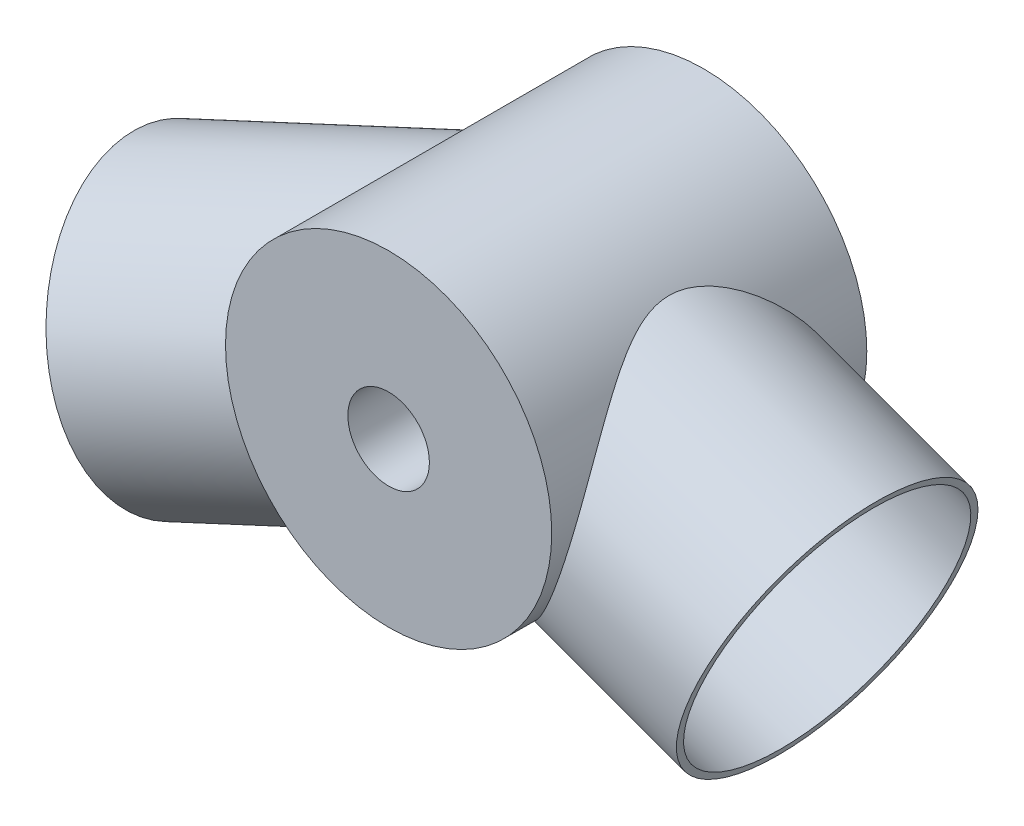
SolidWorks part; units mm, degrees
material "ABS"
ref_plane "Front Plane" through (0, 0, 0) normal (0, 0, 1) x (1, 0, 0)
ref_plane "Top Plane" through (0, 0, 0) normal (0, 1, 0) x (1, 0, 0)
ref_plane "Right Plane" through (0, 0, 0) normal (1, 0, 0) x (0, 0, -1)
sketch "Sketch1" plane through (0, 0, 0) normal (0, 0, 1) x (1, 0, 0)
  circle A0 centre (0, 0) radius 12
  dimension "D1" = 24
extrude "Boss-Extrude1" add sketch "Sketch1" along normal mid plane 23.18
sketch "Sketch2" plane through (0, 0, 0) normal (1, 0, 0) x (0, 0, -1)
  line L0 (-11.59, 0) -> (11.59, 0) construction
  line L1 (11.59, -12) -> (11.59, 12) construction
  point P6 (0, 0)
ref_plane "Plane1" through (0, 0, 0) normal (0.9397, -0.342, 0) x (0, 0, -1)
ref_plane "Plane2" through (0, 0, 0) normal (0.9397, 0.342, 0) x (0, 0, -1)
sketch "Sketch6" plane through (0, 0, 0) normal (0.9397, 0.342, 0) x (0, 0, -1)
  line L0 (0, -12) -> (0, 12) construction
  line L2 (11.59, 12) -> (-11.59, 12) construction
  point P4 (0, 0)
ref_plane "Plane3" through (0, 0, 0) normal (0.9254, 0.3368, -0.1736) x (-0.342, 0.9397, 0)
sketch "Sketch8" plane through (0, 0, 0) normal (0.9254, 0.3368, -0.1736) x (-0.342, 0.9397, 0)
  circle A0 centre (0, -1.5) radius 10
  dimension "D1" = 20
  dimension "D2" = 1.5
extrude "Extrude-Thin2" add sketch "Sketch8" against normal blind 22 from offset 4.1 thin offset against normal yes
sketch "Sketch3" plane through (0, 0, 0) normal (0.9397, -0.342, 0) x (0, 0, -1)
  circle A0 centre (0, 0) radius 10
  dimension "D1" = 20
extrude "Extrude-Thin1" add sketch "Sketch3" along normal blind 22 thin
sketch "Sketch4" plane through (0, 0, -11.59) normal (0, 0, -1) x (-1, 0, 0)
  circle A0 centre (0, 0) radius 7.5
  dimension "D1" = 15
extrude "Cut-Extrude1" cut sketch "Sketch4" against normal blind 10
sketch "Sketch5" plane through (0, 0, 11.59) normal (0, 0, 1) x (1, 0, 0)
  circle A0 centre (0, 0) radius 3
  dimension "D1" = 6
extrude "Cut-Extrude2" cut sketch "Sketch5" against normal through all
mirror "Mirror1" [suppressed]
delete or keep bodies "Body-Delete/Keep 1" [suppressed] type delete bodies bodies 105
